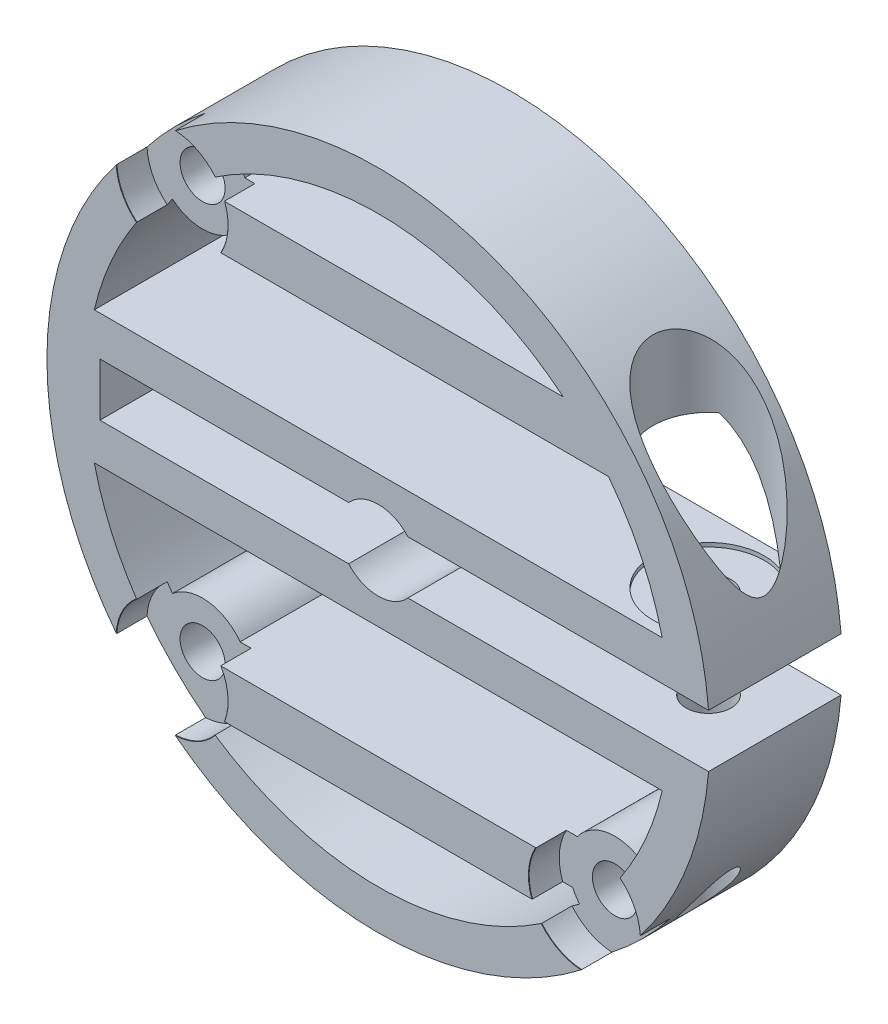
SolidWorks part; units mm, degrees
ref_plane "Front Plane" through (0, 0, 0) normal (0, 0, 1) x (1, 0, 0)
ref_plane "Top Plane" through (0, 0, 0) normal (0, 1, 0) x (1, 0, 0)
ref_plane "Right Plane" through (0, 0, 0) normal (1, 0, 0) x (0, 0, -1)
sketch "Sketch1" plane through (0, 0, 0) normal (0, 0, 1) x (1, 0, 0)
  line L0 (-25, 0) -> (25, 0) construction
  line L2 (-21, -2) -> (25, -2)
  line L3 (-21, -2) -> (-21, 2)
  line L4 (-21, 2) -> (25, 2)
  line L5 (25, -2) -> (25, 2)
  circle A0 centre (0, 0) radius 3
  circle A1 centre (0, 0) radius 25
  point P6 (0, 0)
  dimension "D1" = 6
  dimension "D2" = 50
  dimension "D3" = 4
  dimension "D4" = 21
extrude "Boss-Extrude1" add sketch "Sketch1" along normal blind 10 contours A1 L0 L3 L4 A0 | L0 A1 L2 A0 L3
sketch "Sketch2" plane through (0, 0, 10) normal (0, 0, 1) x (1, 0, 0)
  line L0 (-22, 0) -> (22, 0) construction
  line L1 (0, 0) -> (15.5563, 15.5563) construction
  line L2 (0, 0) -> (15.5563, -15.5563) construction
  line L3 (0, 0) -> (-15.5563, -15.5563) construction
  line L4 (0, 0) -> (-15.5563, 15.5563) construction
  circle A0 centre (0, 0) radius 22 construction
  arc A1 (24.9199, 2) -> (24.9199, -2) centre (0, 0) ccw construction
  point P8 (0, 0)
  point P16 (0, 0)
  dimension "D1" = 3
  dimension "D2" = 45
  dimension "D3" = 4
ref_plane "Plane1" through (0, 22, 0) normal (0, -1, 0) x (-1, 0, 0)
sketch "Sketch3" plane through (0, 22, 0) normal (0, -1, 0) x (-1, 0, 0)
  line L0 (-14.9199, 0) -> (-24.9199, -10) construction
  line L1 (-14.9199, -10) -> (-24.9199, 0) construction
  line L8 (-14.9199, 0) -> (-24.9199, 0)
  line L9 (-14.9199, -10) -> (-14.9199, 0)
  line L10 (-24.9199, -10) -> (-14.9199, -10)
  line L11 (-24.9199, 0) -> (-24.9199, -10)
  point P2 (-19.9199, -5)
  dimension "D1" = 10
  dimension "D2" = 10
hole_wizard "CBORE for M3 Hex Head Machine Screw2" positions "Sketch5" profile "Sketch6" counterbore size "M3" standard "ANSI Metric" end condition through all
sketch "Sketch5" plane through (0, 22, 0) normal (0, -1, 0) x (-1, 0, 0)
  point P0 (-19.9199, -5)
sketch "Sketch6" plane through (19.9199, 22, 5) normal (1, 0, 0) x (0, 0, 1)
  line L0 (0, 0) -> (0, 47)
  line L1 (0, 47) -> (1.7, 47)
  line L3 (1.7, 47) -> (1.7, 17.3)
  line L4 (4.2, 17.3) -> (1.7, 17.3)
  line L5 (4.2, 17.3) -> (4.2, 0.025)
  line L6 (4.2, 0.025) -> (4.225, 0)
  line L7 (4.225, 0) -> (0, 0)
  line L8 (-4.2, 0.025) -> (-4.225, 0) construction
  line L11 (0, -6.35) -> (0, 107.95) construction
  dimension "Thru Hole Dia." = 3.4
  dimension "Thru Hole Depth" = 47
  dimension "C'Bore Dia." = 8.4
  dimension "C'Bore Depth" = 17.3
  dimension "Near C'Sink Dia." = 8.45
  dimension "Near C'Sink Angle" = 90
hole_wizard "CBORE for M3 Hex Head Machine Screw3" positions "Sketch7" profile "Sketch8" counterbore size "M3" standard "ANSI Metric" end condition through all
sketch "Sketch7" plane through (-11.2763, -30.4367, 10) normal (0, 0, 1) x (1, 0, 0)
  point P3 (-4.2801, 45.993)
  point P6 (-4.2801, 14.8804)
  point P9 (26.8326, 14.8804)
  point P14 (0, 0)
sketch "Sketch8" plane through (-15.5563, 15.5563, 10) normal (1, 0, 0) x (0, -1, 0)
  line L0 (0, 0) -> (0, 10)
  line L1 (0, 10) -> (1.7, 10)
  line L2 (1.7, 10) -> (1.7, 2.3)
  line L3 (4.2, 2.3) -> (1.7, 2.3)
  line L4 (4.2, 2.3) -> (4.2, 0.025)
  line L5 (4.2, 0.025) -> (4.225, 0)
  line L6 (4.225, 0) -> (0, 0)
  line L7 (-4.2, 0.025) -> (-4.225, 0) construction
  line L8 (0, -6.35) -> (0, 107.95) construction
  dimension "Thru Hole Dia." = 3.4
  dimension "Thru Hole Depth" = 10
  dimension "C'Bore Dia." = 8.4
  dimension "C'Bore Depth" = 2.3
  dimension "Near C'Sink Dia." = 8.45
  dimension "Near C'Sink Angle" = 90
sketch "Sketch9" plane through (0, 0, 0) normal (0, 0, -1) x (-1, 0, 0)
  line L0 (-21.4243, 5) -> (21.4243, 5)
  line L1 (-17.371, 13.5) -> (17.371, 13.5)
  line L2 (-21.4243, -5) -> (21.4243, -5)
  line L3 (-17.371, -13.5) -> (17.371, -13.5)
  line L4 (-2.2361, 2) -> (-24.9199, 2) construction
  line L5 (-2.2361, -2) -> (-24.9199, -2) construction
  line L6 (13.9642, 17) -> (-13.9642, 17)
  line L7 (-13.9642, -17) -> (13.9642, -17)
  circle A0 centre (0, 0) radius 22
  circle A1 centre (0, 0) radius 22 construction
  circle A3 centre (15.5563, -15.5563) radius 3.5
  circle A4 centre (15.5563, 15.5563) radius 3.5
  circle A5 centre (-15.5563, -15.5563) radius 3.5
  dimension "D7" = 7
  dimension "D1" = 3
  dimension "D2" = 3
  dimension "D3" = 8.5
  dimension "D4" = 8.5
  dimension "D5" = 3.5
  dimension "D6" = 3.5
extrude "Cut-Extrude1" cut sketch "Sketch9" against normal up to next contours A5 A0 A3 L7 | A5 L3 A3 A0 L2 | A4 L1 A0 L0 | A4 A0 L6
